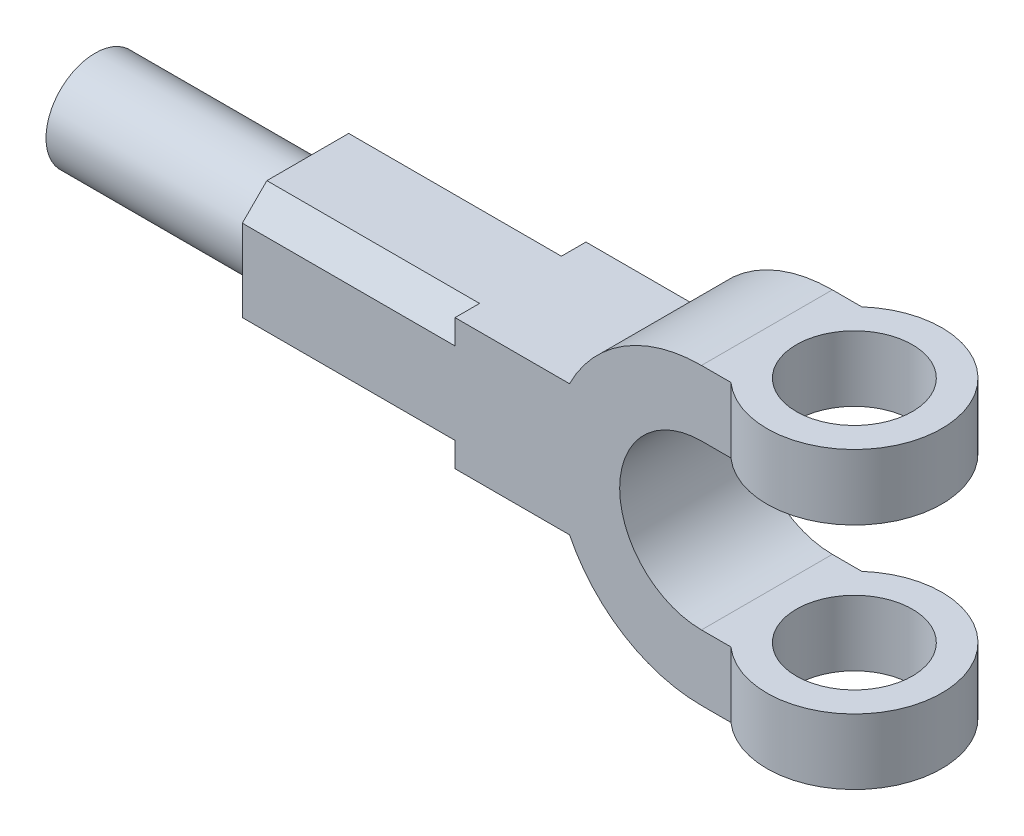
SolidWorks part; units mm, degrees
ref_plane "Front Plane" through (0, 0, 0) normal (0, 0, 1) x (1, 0, 0)
ref_plane "Top Plane" through (0, 0, 0) normal (0, 1, 0) x (1, 0, 0)
ref_plane "Right Plane" through (0, 0, 0) normal (1, 0, 0) x (0, 0, -1)
sketch "Sketch1" plane through (0, 0, 0) normal (0, 0, 1) x (1, 0, 0)
  line L0 (0, 25) -> (9, 25)
  line L1 (9, 25) -> (9, 45)
  line L2 (9, 45) -> (0, 45)
  line L3 (0, -45) -> (9, -45)
  line L4 (9, -45) -> (9, -25)
  line L5 (9, -25) -> (0, -25)
  line L6 (-140.3113, 0) -> (0, 0) construction
  line L7 (-40.3113, 20) -> (-140.3113, 20)
  line L9 (-40.3113, -20) -> (-140.3113, -20)
  line L10 (-140.3113, 20) -> (-140.3113, -20)
  arc A0 (0, 25) -> (0, -25) centre (0, 0) ccw
  arc A1 (0, 45) -> (0, -45) centre (0, 0) ccw
  dimension "D1" = 25
  dimension "D2" = 20
  dimension "D3" = 9
  dimension "D4" = 40
  dimension "D5" = 100
extrude "Boss-Extrude1" add sketch "Sketch1" along normal mid plane 40 contours L10 L6 A1 L7 | L6 L10 L9 A1 | A1 L6 A0 L0 L1 L2 | L6 A1 L3 L4 L5 A0
sketch "Sketch2" plane through (0, 45, 0) normal (0, 1, 0) x (1, 0, 0)
  line L0 (9, -20) -> (9, 20) construction
  circle A0 centre (26.7222, 0) radius 26.7222
  circle A1 centre (26.7222, 0) radius 17.7222
extrude "Boss-Extrude2" add sketch "Sketch2" against normal blind 20
mirror "Mirror1" about plane through (0, 0, 0) normal (0, 1, 0) of "Boss-Extrude2"
sketch "Sketch3" plane through (-140.3113, 0, 0) normal (-1, 0, 0) x (0, 0, 1)
  line L0 (20, 20) -> (-20, 20) construction
  line L1 (-20, 20) -> (-20, -20) construction
  line L4 (-12.5, 20) -> (-20, 20)
  line L5 (-20, 20) -> (-20, 12.5)
  line L8 (-12.5, 20) -> (-20, 12.5)
  dimension "D1" = 45
  dimension "D2" = 7.5
extrude "Cut-Extrude1" cut sketch "Sketch3" against normal blind 65
sketch "Sketch4" plane through (-140.3113, 0, 0) normal (-1, 0, 0) x (0, 0, 1)
  circle A0 centre (0, 0) radius 15
  dimension "D1" = 30
extrude "Boss-Extrude3" add sketch "Sketch4" along normal blind 65
pattern_circular "CirPattern1" count 4 over 360 about axis through (0, 0, 0) along (1, 0, 0) of "Cut-Extrude1"
